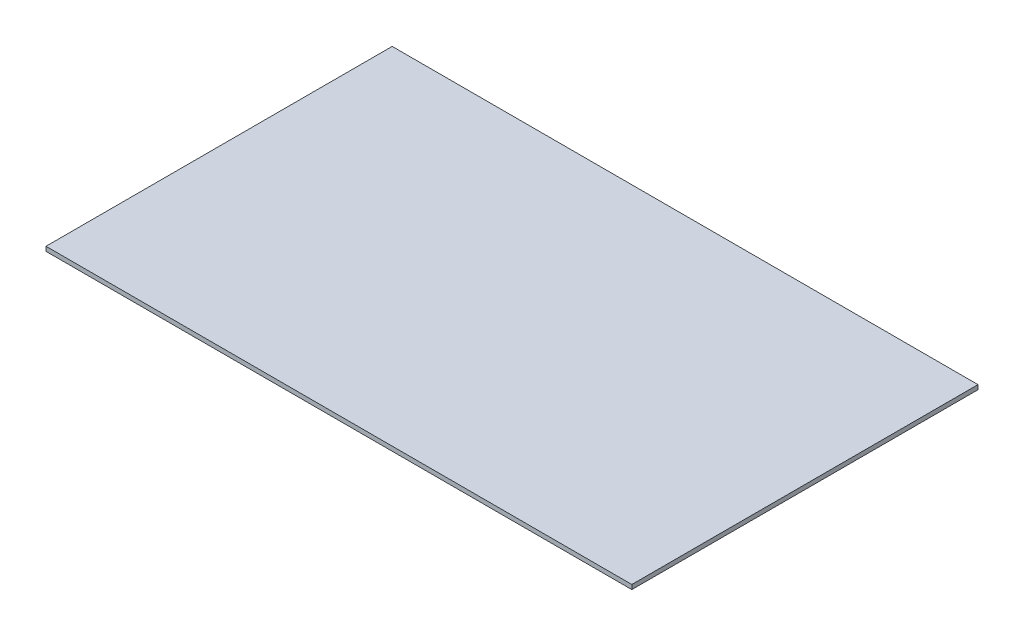
SolidWorks part; units mm, degrees
ref_plane "Front Plane" through (0, 0, 0) normal (0, 0, 1) x (1, 0, 0)
ref_plane "Top Plane" through (0, 0, 0) normal (0, 1, 0) x (1, 0, 0)
ref_plane "Right Plane" through (0, 0, 0) normal (1, 0, 0) x (0, 0, -1)
sketch "Sketch1" plane through (0, 0, 0) normal (0, 1, 0) x (1, 0, 0)
  line L1 (0, 0) -> (3352.8, 0)
  line L2 (0, 0) -> (0, -1981.2)
  line L3 (0, -1981.2) -> (3352.8, -1981.2)
  line L4 (3352.8, 0) -> (3352.8, -1981.2)
  point P5 (0, 0)
extrude "Boss-Extrude1" add sketch "Sketch1" along normal blind 25.4
